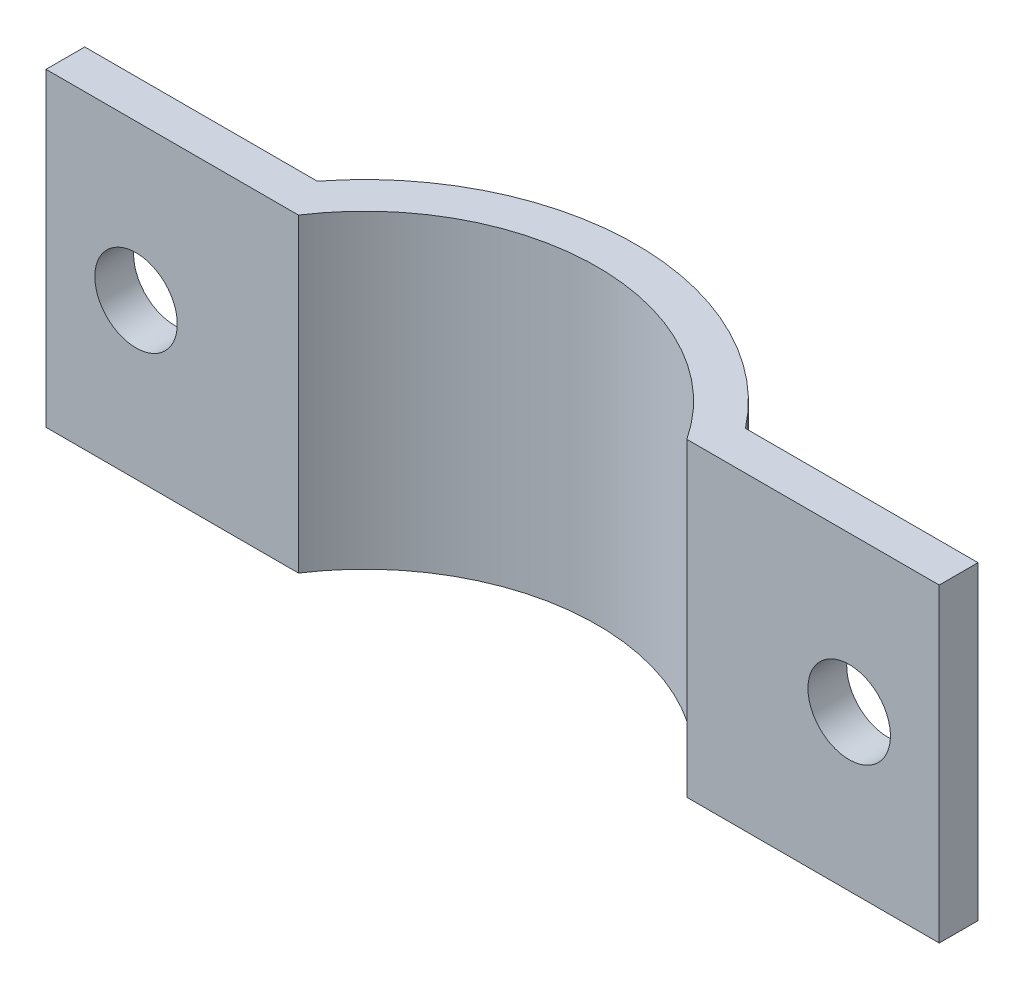
SolidWorks part; units mm, degrees
ref_plane "Front Plane" through (0, 0, 0) normal (0, 0, 1) x (1, 0, 0)
ref_plane "Top Plane" through (0, 0, 0) normal (0, 1, 0) x (1, 0, 0)
ref_plane "Right Plane" through (0, 0, 0) normal (1, 0, 0) x (0, 0, -1)
sketch "Sketch1" plane through (0, 0, 0) normal (0, 1, 0) x (1, 0, 0)
  line L0 (0, 0) -> (32.2155, 0) construction
  line L1 (0, 8.89) -> (38.1, 8.89) construction
  line L2 (0, 0) -> (0, 41.8211) construction
  line L3 (-36.5874, 13.6525) -> (36.5874, 13.6525) construction
  line L4 (-36.5874, 4.1275) -> (36.5874, 4.1275) construction
  line L5 (36.5874, 13.6525) -> (17.5374, 13.6525)
  line L6 (36.5874, 13.6525) -> (36.5874, 4.1275)
  line L7 (36.5874, 4.1275) -> (21.8384, 4.1275)
  line L8 (-17.5374, 13.6525) -> (-36.5874, 13.6525)
  line L9 (-36.5874, 13.6525) -> (-36.5874, 4.1275)
  line L10 (-36.5874, 4.1275) -> (-21.8384, 4.1275)
  circle A0 centre (0, 0) radius 19.05
  circle A1 centre (0, 0) radius 22.225 construction
  arc A3 (-21.8384, 4.1275) -> (21.8384, 4.1275) centre (0, 0) ccw
  arc A5 (17.5374, 13.6525) -> (-17.5374, 13.6525) centre (0, 0) ccw
  point P13 (0, 13.6525)
  point P14 (0, 4.1275)
  dimension "D1" = 38.1
  dimension "D2" = 44.45
  dimension "D3" = 8.89
  dimension "D4" = 38.1
  dimension "D5" = 4.7625
  dimension "D6" = 19.05
extrude "Boss-Extrude1" add sketch "Sketch1" along normal blind 25.4
sketch "Sketch2" plane through (0, 0, -13.6525) normal (0, 0, -1) x (-1, 0, 0)
  line L3 (36.5874, 12.7) -> (17.5374, 12.7) construction
  line L4 (36.5874, 25.4) -> (36.5874, 0) construction
  line L5 (17.5374, 25.4) -> (17.5374, 0) construction
  line L6 (0, 0) -> (0, 25.4) construction
  line L7 (-17.5374, 0) -> (17.5374, 0) construction
  line L8 (17.5374, 25.4) -> (-17.5374, 25.4) construction
  circle A0 centre (29.21, 12.7) radius 3.3782
  circle A1 centre (-29.21, 12.7) radius 3.3782
  dimension "D1" = 6.7564
  dimension "D2" = 29.21
extrude "Cut-Extrude1" cut sketch "Sketch2" against normal through all
sketch "Sketch3" plane through (0, 25.4, 0) normal (0, 1, 0) x (1, 0, 0)
  line L0 (-36.5874, 8.89) -> (42.4749, 8.89) construction
  line L1 (-36.5874, 13.6525) -> (-36.5874, 4.1275) construction
  line L2 (42.4749, 10.4775) -> (-42.7681, 10.4775) construction
  line L8 (42.4749, 10.4775) -> (-42.7681, 10.4775)
  line L9 (42.4749, 10.4775) -> (42.4749, -23.6747)
  line L10 (42.4749, -23.6747) -> (-42.7681, -23.6747)
  line L11 (-42.7681, 10.4775) -> (-42.7681, -23.6747)
  dimension "D1" = 1.5875
extrude "Cut-Extrude2" cut sketch "Sketch3" against normal through all
